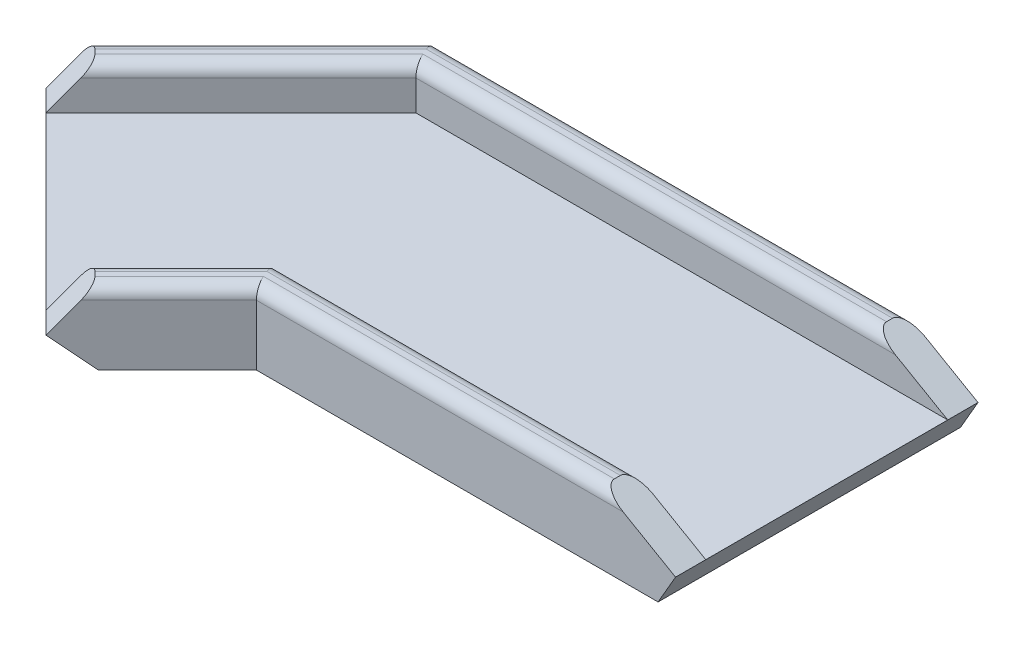
SolidWorks part; units mm, degrees
material "Maple"
ref_plane "Front Plane" through (0, 0, 0) normal (0, 0, 1) x (1, 0, 0)
ref_plane "Top Plane" through (0, 0, 0) normal (0, 1, 0) x (1, 0, 0)
ref_plane "Right Plane" through (0, 0, 0) normal (1, 0, 0) x (0, 0, -1)
sketch "Sketch1" plane through (0, 0, 0) normal (0, 0, 1) x (1, 0, 0)
  line L2 (-57.15, 3.175) -> (57.15, 3.175)
  line L3 (-57.15, 3.175) -> (-57.15, -3.175)
  line L4 (-57.15, -3.175) -> (57.15, -3.175)
  line L5 (57.15, 3.175) -> (57.15, -3.175)
  line L6 (-57.15, 3.175) -> (57.15, -3.175) construction
  line L7 (-57.15, -3.175) -> (57.15, 3.175) construction
  point P1 (0, 0)
  dimension "D1" = 6.35
  dimension "D2" = 114.3
extrude "Boss-Extrude1" add sketch "Sketch1" against normal blind 63.5
sketch "Sketch2" plane through (0, 3.175, 0) normal (0, 1, 0) x (1, 0, 0)
  line L1 (57.15, 63.5) -> (-57.15, 63.5)
  line L2 (57.15, 63.5) -> (57.15, 57.15)
  line L3 (57.15, 57.15) -> (-57.15, 57.15)
  line L4 (-57.15, 63.5) -> (-57.15, 57.15)
  line L5 (57.15, 63.5) -> (57.15, 0) construction
  line L6 (-57.15, 0) -> (57.15, 0)
  line L7 (-57.15, 0) -> (-57.15, 6.35)
  line L8 (-57.15, 6.35) -> (57.15, 6.35)
  line L9 (57.15, 0) -> (57.15, 6.35)
  line L10 (-57.15, 63.5) -> (-57.15, 0) construction
  line L11 (-57.15, 0) -> (57.15, 0) construction
  dimension "D1" = 6.35
  dimension "D2" = 6.35
extrude "Boss-Extrude2" add sketch "Sketch2" along normal blind 8.89
sketch "Sketch3" plane through (0, 0, 0) normal (0, 0, 1) x (1, 0, 0)
  line L0 (57.15, 3.175) -> (41.7521, 12.065)
  line L1 (-57.15, 12.065) -> (57.15, 12.065) construction
  line L2 (41.7521, 12.065) -> (48.5274, 23.8003)
  line L3 (48.5274, 23.8003) -> (66.675, 13.3228)
  line L4 (66.675, 13.3228) -> (57.15, -3.175)
  line L5 (-57.15, -3.175) -> (57.15, -3.175) construction
  line L6 (57.15, 3.175) -> (53.4838, -3.175)
  line L7 (-57.15, -3.175) -> (57.15, -3.175) construction
  line L8 (53.4838, -3.175) -> (56.2335, -4.7625)
  line L9 (57.15, 3.175) -> (-57.15, 3.175) construction
  line L10 (56.2335, -4.7625) -> (57.15, -3.175)
  line L11 (57.15, 3.175) -> (-57.15, 3.175) construction
  point P13 (69.85, 18.822)
  point P15 (0, 0)
  point P18 (57.0096, 3.175)
  dimension "D1" = 30
  dimension "D2" = 19.05
extrude "Cut-Extrude1" cut sketch "Sketch3" against normal through all
sketch "Sketch5" plane through (0, 0, 0) normal (0, 1, 0) x (1, 0, 0)
  line L0 (-57.15, 63.5) -> (-30.8474, 0)
  line L2 (-30.8474, 0) -> (-57.15, 0)
  line L3 (-57.15, 0) -> (-57.15, 63.5)
  dimension "D1" = 22.5
extrude "Cut-Extrude2" cut sketch "Sketch5" against normal through all both and the other way through all
sketch "Sketch9" plane through (0, 0, 0) normal (0, 1, 0) x (1, 0, 0)
  line L0 (-30.8474, 0) -> (-57.15, 63.5) construction
  line L1 (-30.8474, 0) -> (-57.15, 63.5)
  line L2 (-57.15, 63.5) -> (-97.8336, 22.8164)
  line L3 (-97.8336, 22.8164) -> (-52.9323, -22.0848)
  line L4 (-52.9323, -22.0848) -> (-30.8474, 0)
  point P6 (0, 0)
  dimension "D1" = 63.5
  dimension "D2" = 112.5
extrude "Boss-Extrude4" add sketch "Sketch9" along normal mid plane 6.35
sketch "Sketch11" plane through (0, 3.175, 0) normal (0, 1, 0) x (1, 0, 0)
  line L0 (-57.15, 63.5) -> (-97.8336, 22.8164)
  line L1 (-97.8336, 22.8164) -> (-93.3434, 18.3263)
  line L2 (-97.8336, 22.8164) -> (-52.9323, -22.0848) construction
  line L3 (-93.3434, 18.3263) -> (-54.5197, 57.15)
  line L4 (-54.5197, 57.15) -> (-57.15, 63.5)
  line L5 (-33.4777, 6.35) -> (-57.4224, -17.5947)
  line L6 (-57.4224, -17.5947) -> (-52.9323, -22.0848)
  line L7 (-52.9323, -22.0848) -> (-30.8474, 0)
  line L8 (-30.8474, 0) -> (-33.4777, 6.35)
extrude "Boss-Extrude5" add sketch "Sketch11" along normal up to surface (8.89 mm away) up to face at (4.7948, 12.065, -3.175)
fillet "Fillet1" radius 2.54 8 edges at (-41.8899, 12.065, 11.0424) (5.4523, 12.065, 0) (4.1372, 12.065, -6.35) (-45.45, 12.065, 5.6224) (-73.9316, 12.065, -37.7382) (-6.3838, 12.065, -57.15)
sketch "Sketch12" plane through (-15.4237, 0, -15.4237) normal (0.7071, 0, 0.7071) x (0.7071, 0, -0.7071)
  line L0 (-53.0451, 3.175) -> (-45.268, -3.175)
  line L1 (-53.0451, 9.525) -> (-53.0451, -3.175) construction
  line L2 (-53.0451, -3.175) -> (-21.8124, -3.175) construction
  line L3 (-45.268, -3.175) -> (-53.3002, -13.0124)
  line L4 (-53.3002, -13.0124) -> (-72.9749, 3.052)
  line L5 (-72.9749, 3.052) -> (-56.9105, 22.7267)
  line L6 (-56.9105, 22.7267) -> (-45.0129, 13.0124)
  line L7 (-45.0129, 13.0124) -> (-53.0451, 3.175)
  line L8 (32.634, 9.525) -> (40.4112, 3.175) construction
  point P6 (0, 0)
  point P11 (-57.7041, 20.6505)
  point P12 (-56.7919, 18.7263)
  dimension "D1" = 12.7
  dimension "D2" = 25.4
  dimension "D3" = 25.4
extrude "Cut-Extrude3" cut sketch "Sketch12" against normal through all
